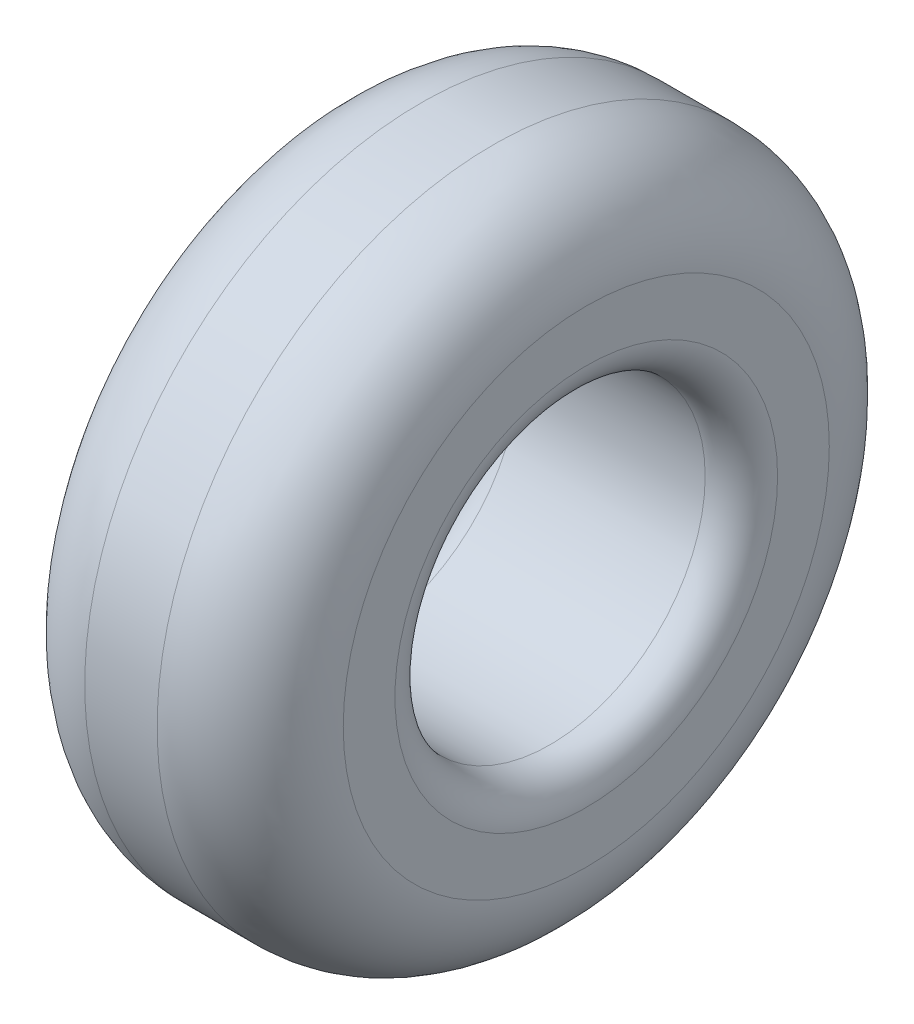
SolidWorks part; units mm, degrees
ref_plane "Front Plane" through (0, 0, 0) normal (0, 0, 1) x (1, 0, 0)
ref_plane "Top Plane" through (0, 0, 0) normal (0, 1, 0) x (1, 0, 0)
ref_plane "Right Plane" through (0, 0, 0) normal (1, 0, 0) x (0, 0, -1)
sketch "Sketch1" plane through (0, 0, 0) normal (1, 0, 0) x (0, 0, -1)
  circle A0 centre (0, 0) radius 165.1
extrude "Boss-Extrude1" add sketch "Sketch1" along normal blind 127
sketch "Sketch2" plane through (127, 0, 0) normal (1, 0, 0) x (0, 0, -1)
  circle A0 centre (0, 0) radius 76.2
extrude "Cut-Extrude2" cut sketch "Sketch2" against normal through all
fillet "Fillet1" radius 17.78 2 edges at (127, 0, -76.2) (0, 0, -76.2)
fillet "Fillet2" radius 45.72 2 edges at (0, 0, -165.1) (127, 0, -165.1)
